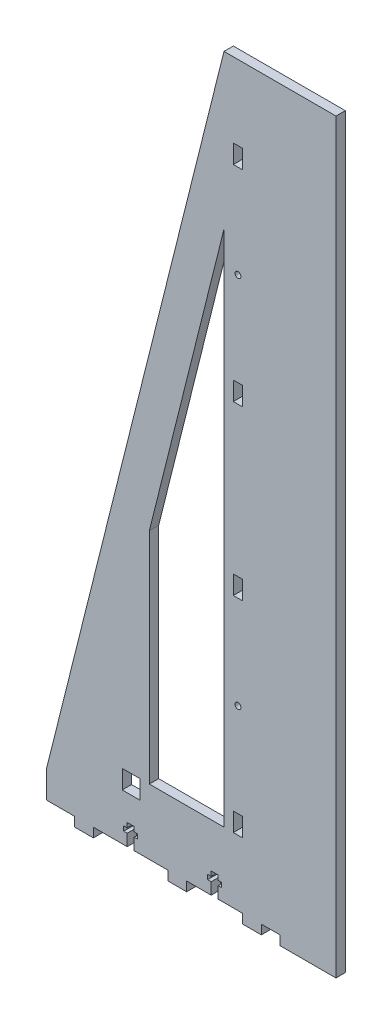
SolidWorks part; units mm, degrees
ref_plane "Front Plane" through (0, 0, 0) normal (0, 0, 1) x (1, 0, 0)
ref_plane "Top Plane" through (0, 0, 0) normal (0, 1, 0) x (1, 0, 0)
ref_plane "Right Plane" through (0, 0, 0) normal (1, 0, 0) x (0, 0, -1)
sketch "Sketch1" plane through (0, 0, 0) normal (0, 0, 1) x (1, 0, 0)
  line L0 (120.65, 50.8) -> (120.65, 403.2731)
  line L2 (190.5, 508) -> (120.65, 508)
  line L3 (0, 6.35) -> (0, 25.4)
  line L4 (0, 25.4) -> (120.65, 508)
  line L6 (19.05, 6.35) -> (0, 6.35)
  line L7 (190.5, 508) -> (196.85, 508)
  line L8 (158.75, 6.35) -> (146.05, 6.35)
  line L9 (158.75, 6.35) -> (158.75, 0)
  line L11 (146.05, 6.35) -> (146.05, 0)
  line L12 (133.35, 6.35) -> (95.25, 6.35)
  line L13 (133.35, 6.35) -> (133.35, 0)
  line L14 (120.65, 50.8) -> (82.55, 50.8)
  line L15 (95.25, 6.35) -> (95.25, 0)
  line L16 (190.5, 0) -> (196.85, 0)
  line L17 (82.55, 6.35) -> (82.55, 0)
  line L18 (82.55, 50.8) -> (82.55, 250.8731)
  line L19 (31.75, 6.35) -> (31.75, 0)
  line L20 (82.55, 250.8731) -> (120.65, 403.2731)
  line L21 (19.05, 6.35) -> (19.05, 0)
  line L22 (19.05, 0) -> (31.75, 0)
  line L23 (196.85, 508) -> (196.85, 0)
  line L24 (158.75, 0) -> (190.5, 0)
  line L25 (133.35, 0) -> (146.05, 0)
  line L26 (82.55, 0) -> (95.25, 0)
  line L28 (31.75, 6.35) -> (82.55, 6.35)
  dimension "D1" = 508
  dimension "D2" = 19.05
  dimension "D3" = 69.85
  dimension "D4" = 44.45
  dimension "D5" = 25.4
  dimension "D7" = 12.7
  dimension "D8" = 12.7
  dimension "D9" = 38.1
  dimension "D10" = 12.7
  dimension "D11" = 50.8
  dimension "D12" = 12.7
  dimension "D14" = 6.35
  dimension "D15" = 6.35
extrude "Boss-Extrude1" add sketch "Sketch1" along normal blind 6.35 contours L14 L18 L20 L0 | L6 L3 L4 L2 L7 L23 L16 L24 L9 L8 L11 L25 L13 L12 L15 L26 L17 L28 L19 L22 L21
sketch "Sketch2" plane through (0, 0, 6.35) normal (0, 0, 1) x (1, 0, 0)
  line L0 (31.75, 6.35) -> (82.55, 6.35) construction
  line L1 (31.75, 6.35) -> (31.75, 0) construction
  line L2 (82.55, 6.35) -> (82.55, 0) construction
  line L3 (95.25, 6.35) -> (95.25, 0) construction
  line L4 (133.35, 6.35) -> (133.35, 0) construction
  line L5 (31.75, 6.35) -> (31.75, 0) construction
  line L6 (59.5312, 6.35) -> (54.7688, 6.35)
  line L7 (82.55, 6.35) -> (82.55, 0) construction
  line L8 (95.25, 6.35) -> (95.25, 0) construction
  line L9 (54.7688, 6.35) -> (54.7688, 14.2875)
  line L10 (61.9125, 17.4625) -> (61.9125, 14.2875)
  line L11 (133.35, 6.35) -> (133.35, 0) construction
  line L17 (59.5313, 20.6375) -> (54.7688, 20.6375)
  line L18 (54.7688, 17.4625) -> (54.7688, 20.6375)
  line L19 (54.7688, 17.4625) -> (52.3875, 17.4625)
  line L21 (54.7688, 14.2875) -> (52.3875, 14.2875)
  line L22 (52.3875, 17.4625) -> (52.3875, 14.2875)
  line L23 (59.5312, 14.2875) -> (61.9125, 14.2875)
  line L25 (59.5313, 17.4625) -> (61.9125, 17.4625)
  line L26 (59.5313, 17.4625) -> (59.5313, 20.6375)
  line L28 (59.5312, 6.35) -> (59.5312, 14.2875)
  line L30 (116.6813, 6.35) -> (111.9188, 6.35)
  line L33 (111.9188, 6.35) -> (111.9188, 14.2875)
  line L34 (119.0625, 17.4625) -> (119.0625, 14.2875)
  line L41 (116.6813, 20.6375) -> (111.9188, 20.6375)
  line L42 (111.9188, 17.4625) -> (111.9188, 20.6375)
  line L43 (111.9188, 17.4625) -> (109.5375, 17.4625)
  line L45 (111.9188, 14.2875) -> (109.5375, 14.2875)
  line L46 (109.5375, 17.4625) -> (109.5375, 14.2875)
  line L47 (116.6813, 14.2875) -> (119.0625, 14.2875)
  line L49 (116.6813, 17.4625) -> (119.0625, 17.4625)
  line L50 (116.6813, 17.4625) -> (116.6813, 20.6375)
  line L52 (116.6813, 6.35) -> (116.6813, 14.2875)
  line L53 (133.35, 6.35) -> (95.25, 6.35) construction
  point P0 (95.25, 3.175)
  point P2 (31.75, 3.175)
  point P5 (82.55, 3.175)
  point P31 (133.35, 3.175)
  dimension "D1" = 50.8
  dimension "D2" = 38.1
  dimension "D3" = 0
  dimension "D4" = 2.3813
  dimension "D5" = 23.0188
  dimension "D6" = 23.0188
  dimension "D7" = 16.6687
  dimension "D8" = 16.6687
  dimension "D10" = 2.3813
  dimension "D14" = 0
extrude "Cut-Extrude1" cut sketch "Sketch2" against normal blind 6.35
sketch "Sketch4" plane through (0, 0, 6.35) normal (0, 0, 1) x (1, 0, 0)
  line L0 (151.618, 254) -> (181.2182, 254)
  line L1 (158.75, 0) -> (196.85, 0) construction
  line L3 (127, 203.2) -> (133.35, 203.2)
  line L4 (127, 203.2) -> (127, 190.5)
  line L5 (127, 190.5) -> (133.35, 190.5)
  line L6 (133.35, 203.2) -> (133.35, 190.5)
  line L7 (127, 63.5) -> (133.35, 63.5)
  line L8 (127, 63.5) -> (127, 50.8)
  line L9 (127, 50.8) -> (133.35, 50.8)
  line L10 (133.35, 63.5) -> (133.35, 50.8)
  line L11 (133.35, 444.5) -> (133.35, 457.2)
  line L12 (127, 457.2) -> (133.35, 457.2)
  line L13 (127, 444.5) -> (127, 457.2)
  line L14 (127, 444.5) -> (133.35, 444.5)
  line L15 (133.35, 304.8) -> (133.35, 317.5)
  line L16 (127, 317.5) -> (133.35, 317.5)
  line L17 (127, 304.8) -> (127, 317.5)
  line L18 (127, 304.8) -> (133.35, 304.8)
  line L20 (120.65, 50.8) -> (120.65, 403.2731) construction
  circle A0 centre (130.175, 127) radius 2
  circle A1 centre (130.175, 381) radius 2
  point P2 (177.8, 0)
  dimension "D10" = 4
  dimension "D11" = 63.5
  dimension "D12" = 9.525
  dimension "D1" = 254
  dimension "D2" = 63.5
  dimension "D3" = 6.35
  dimension "D4" = 6.35
  dimension "D5" = 12.7
  dimension "D6" = 63.5
  dimension "D7" = 6.35
  dimension "D8" = 6.35
  dimension "D9" = 12.7
extrude "Cut-Extrude5" cut sketch "Sketch4" against normal blind 6.35 contours L13 L12 L11 L14 | A1 | L16 L15 L18 L17 | L7 L10 L9 L8 | A0 | L5 L6 L3 L4
sketch "Sketch6" plane through (0, 0, 6.35) normal (0, 0, 1) x (1, 0, 0)
  line L0 (82.55, 0) -> (95.25, 0) construction
  line L1 (57.15, 50.8) -> (63.5, 50.8)
  line L2 (57.15, 50.8) -> (57.15, 38.1)
  line L3 (57.15, 38.1) -> (63.5, 38.1)
  line L4 (63.5, 50.8) -> (63.5, 38.1)
  line L5 (82.55, 6.35) -> (82.55, 0) construction
  dimension "D1" = 38.1
  dimension "D2" = 6.35
  dimension "D3" = 12.7
  dimension "D4" = 19.05
extrude "Cut-Extrude6" cut sketch "Sketch6" against normal blind 6.35
sketch "Sketch7" plane through (0, 0, 6.35) normal (0, 0, 1) x (1, 0, 0)
  line L0 (82.55, 50.8) -> (69.85, 50.8)
  line L1 (82.55, 250.8731) -> (69.85, 200.0731)
  line L2 (82.55, 250.8731) -> (120.65, 403.2731) construction
  line L3 (69.85, 200.0731) -> (69.85, 50.8)
  line L4 (82.55, 50.8) -> (82.55, 250.8731) construction
  line L5 (0, 25.4) -> (120.65, 508) construction
  line L6 (82.55, 250.8731) -> (82.55, 50.8)
  dimension "D1" = 12.7
extrude "Cut-Extrude7" cut sketch "Sketch7" against normal blind 6.35
sketch "Sketch5" plane through (0, 0, 6.35) normal (0, 0, 1) x (1, 0, 0)
  line L0 (82.55, 0) -> (95.25, 0) construction
  line L1 (51.4151, 50.8) -> (57.7651, 50.8)
  line L2 (51.4151, 50.8) -> (51.4151, 38.1)
  line L3 (51.4151, 38.1) -> (57.7651, 38.1)
  line L4 (57.7651, 50.8) -> (57.7651, 38.1)
  dimension "D1" = 38.1
  dimension "D2" = 6.35
  dimension "D3" = 12.7
extrude "Cut-Extrude4" cut sketch "Sketch5" against normal blind 6.35 contours L4 L3 L2 L1
